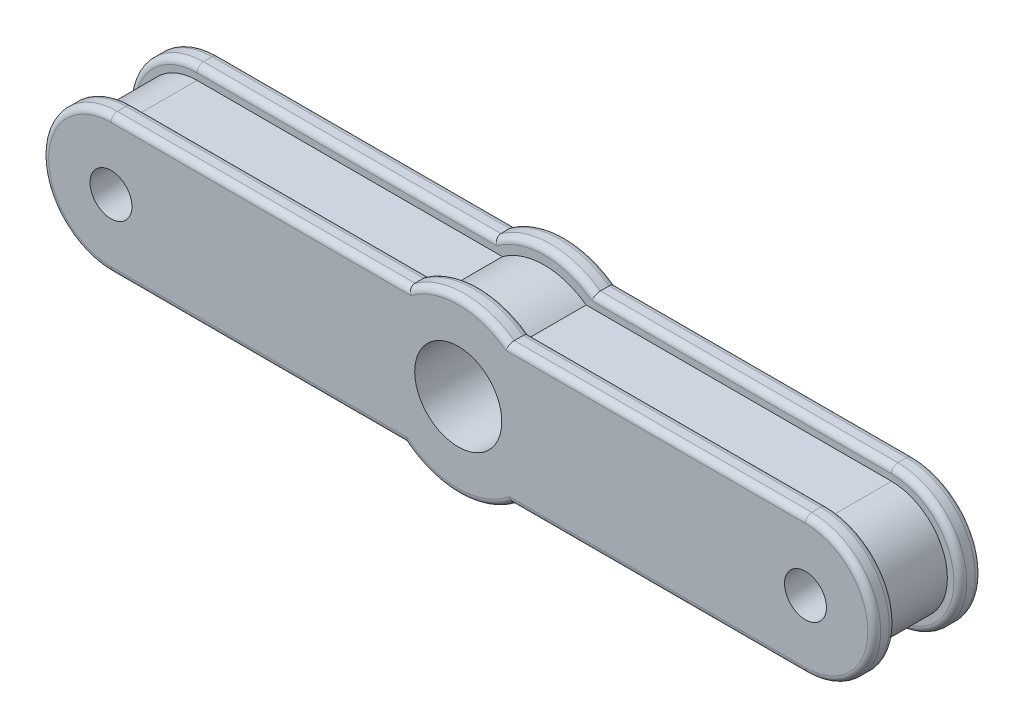
SolidWorks part; units mm, degrees
ref_plane "Front Plane" through (0, 0, 0) normal (0, 0, 1) x (1, 0, 0)
ref_plane "Top Plane" through (0, 0, 0) normal (0, 1, 0) x (1, 0, 0)
ref_plane "Right Plane" through (0, 0, 0) normal (1, 0, 0) x (0, 0, -1)
sketch "Sketch1" plane through (0, 0, 0) normal (0, 0, 1) x (1, 0, 0)
  line L0 (0, 73.4633) -> (0, -67.7758) construction
  line L1 (0, -55) -> (0, 55) construction
  line L2 (-111.2851, 0) -> (140.86, 0) construction
  line L3 (55, 0) -> (-55, 0) construction
  line L4 (-19.481, 26.6362) -> (-161.481, 26.6362)
  line L5 (-161.481, -25.3638) -> (-21.1111, -25.3638)
  line L6 (161.481, -25.3638) -> (21.1111, -25.3638)
  line L7 (19.481, 26.6362) -> (161.481, 26.6362)
  circle A0 centre (0, 0) radius 33
  arc A1 (-161.481, 26.6362) -> (-161.481, -25.3638) centre (-161.481, 0.6362) ccw
  arc A2 (161.481, 26.6362) -> (161.481, -25.3638) centre (161.481, 0.6362) cw
  dimension "D1" = 66
  dimension "D4" = 26
  dimension "D2" = 52
  dimension "D3" = 142
extrude "Boss-Extrude1" add sketch "Sketch1" along normal blind 30 contours L4 A1 L5 A0 | A0 | A2 L7 A0 L6
sketch "Sketch2" plane through (0, 0, 30) normal (0, 0, 1) x (1, 0, 0)
  line L0 (-223.4277, 0) -> (226.6454, 0) construction
  line L1 (16.5, 0) -> (-16.5, 0) construction
  line L2 (-23.1274, 32.6362) -> (-161.481, 32.6362)
  line L3 (-161.481, -31.3638) -> (-24.8257, -31.3638)
  line L4 (0, 93.0454) -> (0, -75.3571) construction
  line L5 (0, -16.5) -> (0, 16.5) construction
  line L6 (161.481, -31.3638) -> (24.8257, -31.3638)
  line L7 (23.1274, 32.6362) -> (161.481, 32.6362)
  circle A0 centre (0, 0) radius 40
  arc A1 (-161.481, 32.6362) -> (-161.481, -31.3638) centre (-161.481, 0.6362) ccw
  arc A2 (-161.481, 26.6362) -> (-161.481, -25.3638) centre (-161.481, 0.6362) ccw construction
  arc A3 (161.481, 32.6362) -> (161.481, -31.3638) centre (161.481, 0.6362) cw
  line M2 (-19.481, 26.6362) -> (-161.481, 26.6362)
  arc M3 (-161.481, 26.6362) -> (-161.481, -25.3638) centre (-161.481, 0.6362) ccw
  line M4 (-161.481, -25.3638) -> (-21.1111, -25.3638)
  arc M5 (-21.1111, -25.3638) -> (21.1111, -25.3638) centre (0, 0) ccw
  line M6 (21.1111, -25.3638) -> (161.481, -25.3638)
  arc M7 (161.481, -25.3638) -> (161.481, 26.6362) centre (161.481, 0.6362) ccw
  line M8 (161.481, 26.6362) -> (19.481, 26.6362)
  arc M9 (19.481, 26.6362) -> (-19.481, 26.6362) centre (0, 0) ccw
  dimension "D1" = 80
  dimension "D2" = 32
  dimension "D3" = 138.3537
  dimension "D4" = 64
extrude "Boss-Extrude4" add sketch "Sketch2" along normal blind 10 contours L2 A1 L3 A0 M4 M3 M2 | A0 M2 M3 M4 | A0 M2 M4 M5 M6 M8 M9 | A0 M8 M2 M9 | A0 M4 M6 M5 | A3 L7 A0 L6 M8 M7 M6 | A0 M6 M7 M8
ref_plane "Plane1" through (0, 0, 15) normal (0, 0, 1) x (1, 0, 0)
mirror "Mirror1" about plane through (0, 0, 15) normal (0, 0, 1) of "Boss-Extrude4"
fillet "Fillet2" radius 3 32 edges at (93.1534, -31.3638, -10) (193.481, 0.6362, -10) (-92.3042, 32.6362, -10) (-193.481, 0.6362, -10) (-93.1534, -31.3638, 0) (-193.481, 0.6362, 0) (93.1534, -31.3638, 0) (193.481, 0.6362, 0) (92.3042, 32.6362, 30) (193.481, 0.6362, 30) (-92.3042, 32.6362, 30) (-193.481, 0.6362, 30) (93.1534, -31.3638, 40) (193.481, 0.6362, 40) (-92.3042, 32.6362, 40) (-193.481, 0.6362, 40) (0, -40, 0) (92.3042, 32.6362, -10) (0, 40, -10) (0, -40, -10) (-93.1534, -31.3638, -10) (-92.3042, 32.6362, 0) (0, 40, 0) (92.3042, 32.6362, 0) (0, 40, 30) (93.1534, -31.3638, 30) (0, -40, 30) (-93.1534, -31.3638, 30) (92.3042, 32.6362, 40) (0, 40, 40) (0, -40, 40) (-93.1534, -31.3638, 40)
hole_wizard "M45 Tapped Hole2" positions "Sketch8" profile "Sketch9" tap size "M45" standard "ISO" end condition through all
sketch "Sketch8" plane through (0, 0, -10) normal (0, 0, -1) x (-1, 0, 0)
  point P0 (0, 0)
sketch "Sketch9" plane through (0, 0, -10) normal (1, 0, 0) x (0, 1, 0)
  line L0 (0, 0) -> (0, 50)
  line L1 (0, 50) -> (20.25, 50)
  line L2 (20.25, 50) -> (20.25, 2.275)
  line L3 (20.25, 2.275) -> (22.525, 0)
  line L5 (22.525, 0) -> (0, 0)
  line L6 (-20.25, 2.275) -> (-22.525, 0) construction
  line L11 (0, -6.35) -> (0, 107.95) construction
  dimension "Thru Tap Drill Dia." = 40.5
  dimension "Thru Tap Drill Depth" = 50
  dimension "Near C'Sink Dia." = 45.05
  dimension "Near C'Sink Angle" = 90
cosmetic thread "Hole Thread2" parameters "D2"=45
hole_wizard "M22 Tapped Hole1" positions "Sketch10" profile "Sketch11" tap size "M22" standard "ISO" end condition through all
sketch "Sketch10" plane through (0, 0, -10) normal (0, 0, -1) x (-1, 0, 0)
  point P0 (-161.481, 0.6362)
  point P3 (161.481, 0.6362)
sketch "Sketch11" plane through (161.481, 0.6362, -10) normal (1, 0, 0) x (0, 1, 0)
  line L0 (0, 0) -> (0, 50)
  line L1 (0, 50) -> (9.75, 50)
  line L2 (9.75, 50) -> (9.75, 1.275)
  line L3 (9.75, 1.275) -> (11.025, 0)
  line L5 (11.025, 0) -> (0, 0)
  line L6 (-9.75, 1.275) -> (-11.025, 0) construction
  line L11 (0, -6.35) -> (0, 107.95) construction
  dimension "Thru Tap Drill Dia." = 19.5
  dimension "Thru Tap Drill Depth" = 50
  dimension "Near C'Sink Dia." = 22.05
  dimension "Near C'Sink Angle" = 90
cosmetic thread "Hole Thread3" parameters "D2"=22
cosmetic thread "Hole Thread4" parameters "D2"=22
